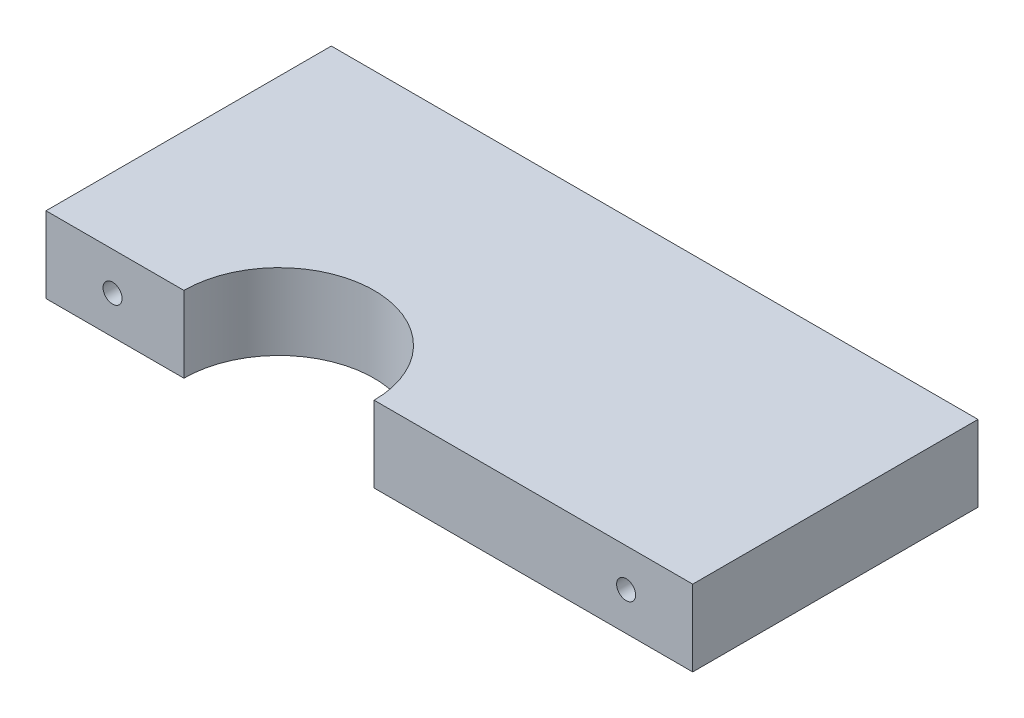
SolidWorks part; units mm, degrees
ref_plane "Front Plane" through (0, 0, 0) normal (0, 0, 1) x (1, 0, 0)
ref_plane "Top Plane" through (0, 0, 0) normal (0, 1, 0) x (1, 0, 0)
ref_plane "Right Plane" through (0, 0, 0) normal (1, 0, 0) x (0, 0, -1)
sketch "Sketch1" plane through (0, 0, 0) normal (0, 1, 0) x (1, 0, 0)
  line L0 (-16.4677, 50.8602) -> (-16.4677, 7.2043) construction
  line L1 (-40.9677, 27.2043) -> (27.0323, 27.2043)
  line L2 (-40.9677, 27.2043) -> (-40.9677, -2.7957)
  line L3 (-40.9677, -2.7957) -> (-26.4677, -2.7957)
  line L4 (27.0323, 27.2043) -> (27.0323, -2.7957)
  line L5 (-6.4677, -2.7957) -> (27.0323, -2.7957)
  line L6 (-16.4677, -2.7957) -> (-16.4677, -58.8172) construction
  arc A0 (-6.4677, -2.7957) -> (-26.4677, -2.7957) centre (-16.4677, -2.7957) ccw
  dimension "D4" = 30
  dimension "D1" = 30
  dimension "D2" = 68
  dimension "D3" = 24.5
extrude "Boss-Extrude1" add sketch "Sketch1" along normal blind 8
sketch "Sketch2" plane through (0, 0, 0) normal (0, 0, 1) x (1, 0, 0)
  line L0 (-40.9677, 4) -> (27.0323, 4) construction
  line L1 (-40.9677, 8) -> (-40.9677, 0) construction
  line L2 (27.0323, 8) -> (27.0323, 0) construction
  circle A0 centre (-33.9677, 4) radius 1
  circle A1 centre (20.0323, 4) radius 1
  dimension "D1" = 2
  dimension "D2" = 2
  dimension "D3" = 7
  dimension "D4" = 7
extrude "Cut-Extrude5" cut sketch "Sketch2" against normal blind 5 from offset 4
sketch "Sketch3" plane through (0, 0, 0) normal (0, 0, 1) x (1, 0, 0)
  line L0 (27.0323, 8) -> (27.0323, 0) construction
  line L1 (-40.9677, 8) -> (-40.9677, 0) construction
  circle A0 centre (17.0323, 4) radius 1
  circle A1 centre (-30.9677, 4) radius 1
  point P8 (-40.9677, 4)
  dimension "D1" = 2
  dimension "D2" = 2
  dimension "D3" = 10
  dimension "D4" = 10
extrude "Cut-Extrude6" cut sketch "Sketch3" along normal blind 10 from surface at -27.2043 starting at face at (-6.9677, 4, -27.2043)
